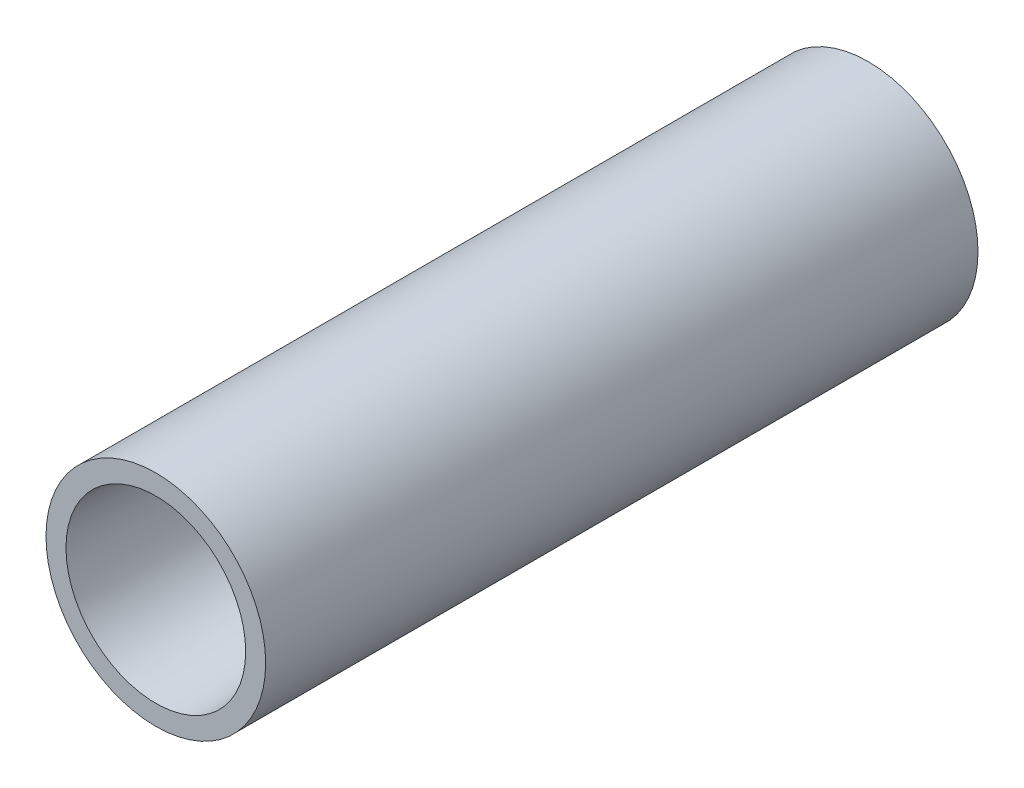
SolidWorks part; units mm, degrees
ref_plane "Front Plane" through (0, 0, 0) normal (0, 0, 1) x (1, 0, 0)
ref_plane "Top Plane" through (0, 0, 0) normal (0, 1, 0) x (1, 0, 0)
ref_plane "Right Plane" through (0, 0, 0) normal (1, 0, 0) x (0, 0, -1)
sketch "Sketch1" plane through (0, 0, 0) normal (0, 0, 1) x (1, 0, 0)
  circle A0 centre (0, 0) radius 2.775
  dimension "D1" = 5.55
extrude "Boss-Extrude1" add sketch "Sketch1" along normal blind 18
sketch "Sketch2" plane through (0, 0, 0) normal (0, 0, 1) x (1, 0, 0)
  circle A0 centre (0, 0) radius 2.27
  dimension "D1" = 4.54
extrude "Cut-Extrude1" cut sketch "Sketch2" along a picked direction on the side of the normal blind 5.68 draft 3.074
sketch "Sketch7" plane through (0, 0, 0) normal (0, 0, 1) x (1, 0, 0)
  circle A0 centre (0, 0) radius 1
extrude "Cut-Extrude2" cut sketch "Sketch7" along normal through all
sketch "Sketch9" plane through (0, 0, 18) normal (0, 0, 1) x (1, 0, 0)
  circle A0 centre (0, 0) radius 2.27
  circle A1 centre (0, 0) radius 2.27 construction
extrude "Cut-Extrude3" cut sketch "Sketch9" against normal blind 5.68 draft 3.074
